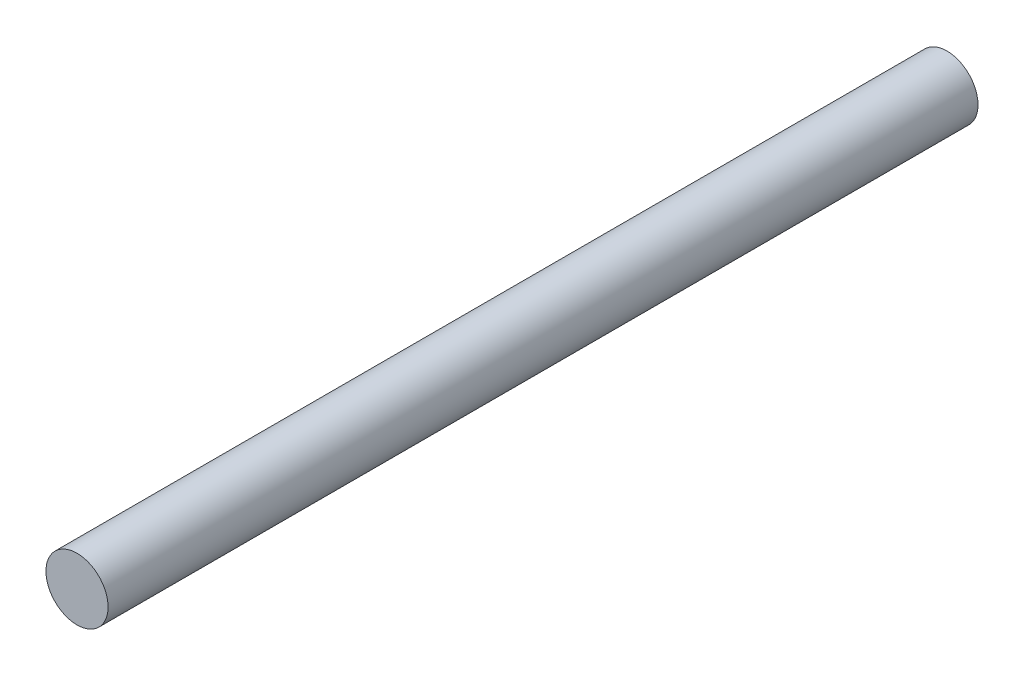
SolidWorks part; units mm, degrees
ref_plane "Front Plane" through (0, 0, 0) normal (0, 0, 1) x (1, 0, 0)
ref_plane "Top Plane" through (0, 0, 0) normal (0, 1, 0) x (1, 0, 0)
ref_plane "Right Plane" through (0, 0, 0) normal (1, 0, 0) x (0, 0, -1)
sketch "Sketch1" plane through (0, 0, 0) normal (0, 0, 1) x (1, 0, 0)
  circle A0 centre (0, 0) radius 3.175
  dimension "D1" = 6.35
extrude "Boss-Extrude1" add sketch "Sketch1" along normal blind 88.9
